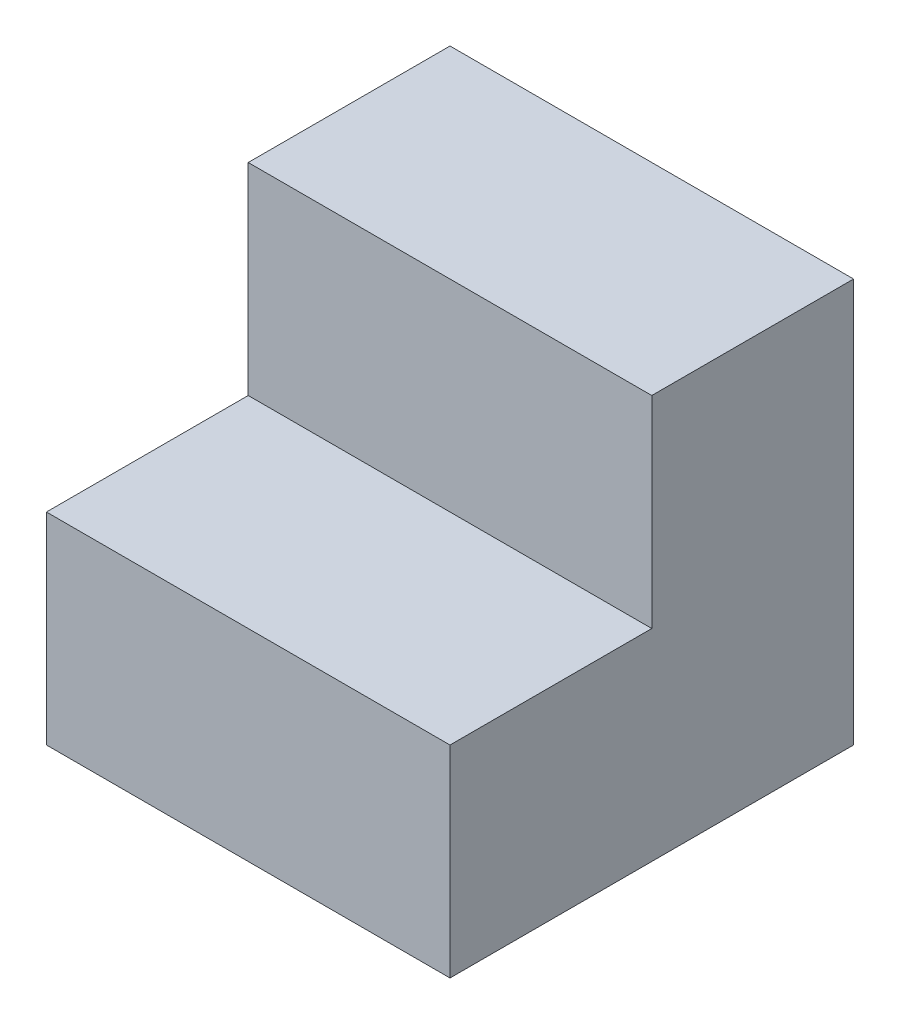
SolidWorks part; units mm, degrees
ref_plane "Front Plane" through (0, 0, 0) normal (0, 0, 1) x (1, 0, 0)
ref_plane "Top Plane" through (0, 0, 0) normal (0, 1, 0) x (1, 0, 0)
ref_plane "Right Plane" through (0, 0, 0) normal (1, 0, 0) x (0, 0, -1)
sketch "Sketch2" plane through (0, 0, 0) normal (1, 0, 0) x (0, 0, -1)
  line L0 (0, 80) -> (0, 0)
  line L1 (0, 55) -> (0, -55) construction
  line L2 (0, 0) -> (-80, 0)
  line L3 (-40, 80) -> (-40, 40)
  line L4 (-40, 40) -> (-80, 40)
  line L5 (0, 80) -> (-40, 80)
  line L6 (-80, 0) -> (-80, 40)
  dimension "D1" = 80
  dimension "D2" = 80
  dimension "D3" = 40
extrude "Boss-Extrude1" add sketch "Sketch2" along normal mid plane 80
